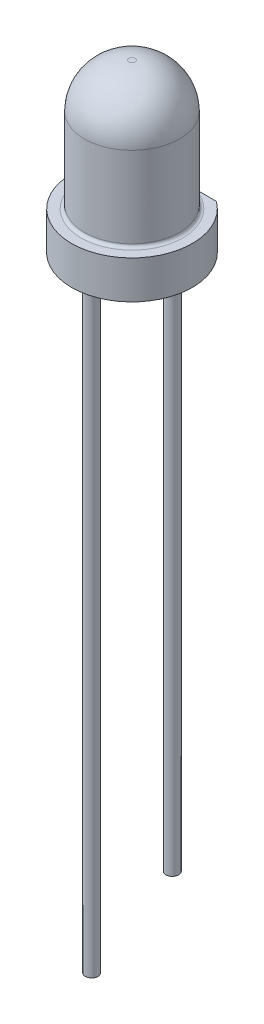
SolidWorks part; units mm, degrees
material "ABS"
ref_plane "Front Plane" through (0, 0, 0) normal (0, 0, 1) x (1, 0, 0)
ref_plane "Top Plane" through (0, 0, 0) normal (0, 1, 0) x (1, 0, 0)
ref_plane "Right Plane" through (0, 0, 0) normal (1, 0, 0) x (0, 0, -1)
sketch "Sketch1" plane through (0, 0, 0) normal (0, 0, 1) x (1, 0, 0)
  line L0 (0, 0) -> (0, 5.25)
  line L1 (0, 0) -> (1.9, 0)
  line L2 (1.9, 0) -> (1.9, 1.2)
  line L3 (1.9, 1.2) -> (1.5, 1.2)
  line L4 (1.5, 1.2) -> (1.5, 3.85)
  line L5 (1.5, 3.85) -> (1.5, 5.25) construction
  line L6 (1.5, 5.25) -> (0.1, 5.25) construction
  line L7 (0.1, 5.25) -> (0, 5.25)
  arc A0 (0.1, 5.25) -> (1.5, 3.85) centre (0.1, 3.85) cw
  dimension "D5" = 1.4
  dimension "D1" = 5.25
  dimension "D2" = 1.2
  dimension "D3" = 1.9
  dimension "D4" = 1.5
revolve "Revolve1" add sketch "Sketch1" angle 360 about L0
sketch "Sketch2" plane through (0, 1.2, 0) normal (0, 1, 0) x (1, 0, 0)
  line L0 (0, 0) -> (0, 1.53) construction
  line L2 (-1.5, 2.03) -> (1.5, 2.03)
  line L3 (-1.5, 2.03) -> (-1.5, 1.53)
  line L4 (-1.5, 1.53) -> (1.5, 1.53)
  line L5 (1.5, 2.03) -> (1.5, 1.53)
  dimension "D1" = 3
  dimension "D2" = 0.5
  dimension "D3" = 1.53
extrude "Cut-Extrude1" cut sketch "Sketch2" against normal up to surface (1.2 mm away) up to face at (0, 0, -1.9)
fillet "Fillet1" radius 0.1 3 edges at (-1.1265, 0.6, -1.53) (1.1265, 0.6, -1.53) (0, 1.2, -1.5)
sketch "Sketch3" plane through (0, 0, 0) normal (0, -1, 0) x (1, 0, 0)
  line L0 (0, 1.27) -> (0, -1.27) construction
  circle A0 centre (0, 1.27) radius 0.2
  circle A1 centre (0, -1.27) radius 0.2
  dimension "D2" = 0.4
  dimension "D1" = 2.54
extrude "Boss-Extrude1" add sketch "Sketch3" along normal blind 17.5
sketch "Sketch4" plane through (0, -17.5, 0) normal (0, -1, 0) x (1, 0, 0)
  circle A1 centre (0, 1.27) radius 0.2
  circle A2 centre (0, 1.27) radius 0.2
  dimension "D1" = 0
extrude "Boss-Extrude2" add sketch "Sketch4" along normal blind 1.5
